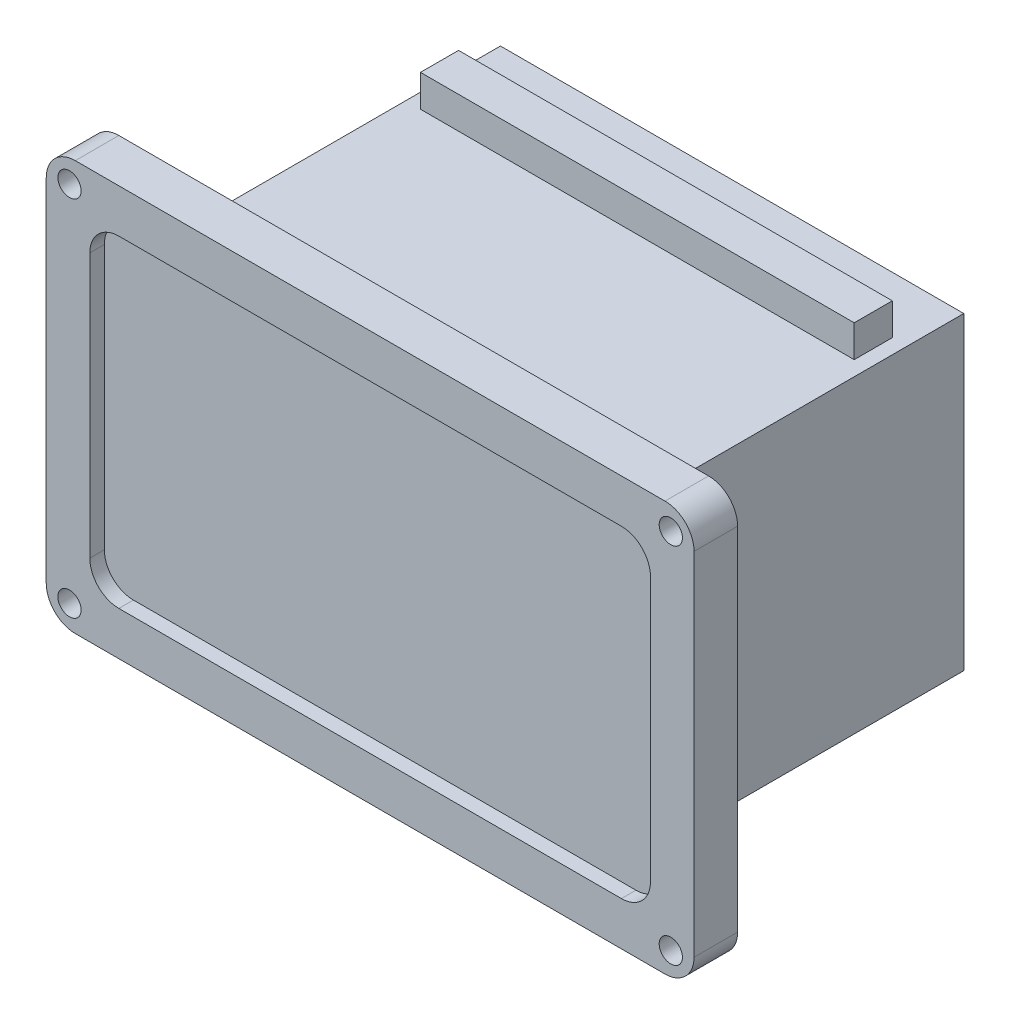
SolidWorks part; units mm, degrees
ref_plane "Alzado" through (0, 0, 0) normal (0, 0, 1) x (1, 0, 0)
ref_plane "Planta" through (0, 0, 0) normal (0, 1, 0) x (1, 0, 0)
ref_plane "Vista lateral" through (0, 0, 0) normal (1, 0, 0) x (0, 0, -1)
sketch "Croquis1" plane through (0, 0, 0) normal (0, 0, 1) x (1, 0, 0)
  line L1 (-101.5, -70.5) -> (101.5, -70.5)
  line L2 (-111.5, -60.5) -> (-111.5, 60.5)
  line L3 (-101.5, 70.5) -> (101.5, 70.5)
  line L4 (111.5, -60.5) -> (111.5, 60.5)
  line L5 (-111.5, -70.5) -> (111.5, 70.5) construction
  line L6 (-111.5, 70.5) -> (111.5, -70.5) construction
  arc A0 (-101.5, -70.5) -> (-111.5, -60.5) centre (-101.5, -60.5) cw
  arc A1 (101.5, -70.5) -> (111.5, -60.5) centre (101.5, -60.5) ccw
  arc A2 (101.5, 70.5) -> (111.5, 60.5) centre (101.5, 60.5) cw
  arc A3 (-111.5, 60.5) -> (-101.5, 70.5) centre (-101.5, 60.5) cw
  point P0 (0, 0)
  dimension "D3" = 10
  dimension "D1" = 223
  dimension "D2" = 141
extrude "Saliente-Extruir1" add sketch "Croquis1" along normal blind 15
sketch "Croquis2" plane through (0, 0, 0) normal (0, 0, -1) x (-1, 0, 0)
  line L0 (-101.5, 70.5) -> (101.5, 70.5) construction
  line L1 (-79.75, -53.25) -> (79.75, -53.25)
  line L2 (-79.75, -53.25) -> (-79.75, 53.25)
  line L3 (-79.75, 53.25) -> (79.75, 53.25)
  line L4 (79.75, -53.25) -> (79.75, 53.25)
  line L5 (-79.75, -53.25) -> (79.75, 53.25) construction
  line L6 (-79.75, 53.25) -> (79.75, -53.25) construction
  point P0 (0, 0)
  dimension "D1" = 106.5
  dimension "D2" = 159.5
  dimension "D3" = 17.25
extrude "Saliente-Extruir2" add sketch "Croquis2" along normal blind 109.6
sketch "Croquis3" plane through (0, 0, 15) normal (0, 0, 1) x (1, 0, 0)
  line L0 (-111.5, 60.5) -> (-111.5, -60.5) construction
  line L1 (86.5, -55.5) -> (-86.5, -55.5)
  line L2 (96.5, -45.5) -> (96.5, 45.5)
  line L3 (86.5, 55.5) -> (-86.5, 55.5)
  line L4 (-96.5, -45.5) -> (-96.5, 45.5)
  line L5 (96.5, -55.5) -> (-96.5, 55.5) construction
  line L6 (96.5, 55.5) -> (-96.5, -55.5) construction
  line L7 (101.5, 70.5) -> (-101.5, 70.5) construction
  arc A0 (-86.5, -55.5) -> (-96.5, -45.5) centre (-86.5, -45.5) cw
  arc A1 (86.5, -55.5) -> (96.5, -45.5) centre (86.5, -45.5) ccw
  arc A2 (96.5, 45.5) -> (86.5, 55.5) centre (86.5, 45.5) ccw
  arc A3 (-86.5, 55.5) -> (-96.5, 45.5) centre (-86.5, 45.5) ccw
  point P0 (0, 0)
  dimension "D3" = 10
  dimension "D1" = 15
  dimension "D2" = 15
extrude "Cortar-Extruir1" cut sketch "Croquis3" against normal blind 5
sketch "Croquis4" plane through (0, 0, 15) normal (0, 0, 1) x (1, 0, 0)
  line L0 (0, 0) -> (-143.5809, 0) construction
  line L1 (0, 0) -> (0, 70.5) construction
  line L2 (101.5, 70.5) -> (-101.5, 70.5) construction
  circle A0 centre (-103.5, 62.5) radius 4
  circle A1 centre (103.5, 62.5) radius 4
  circle A2 centre (103.5, -62.5) radius 4
  circle A3 centre (-103.5, -62.5) radius 4
  dimension "D3" = 8
  dimension "D4" = 8
  dimension "D1" = 62.5
  dimension "D2" = 103.5
extrude "Cortar-Extruir2" cut sketch "Croquis4" against normal blind 15
sketch "Croquis5" plane through (0, 53.25, 0) normal (0, 1, 0) x (1, 0, 0)
  line L1 (-74.6572, 76.9808) -> (74.6572, 76.9808)
  line L2 (-74.6572, 76.9808) -> (-74.6572, 90.0913)
  line L3 (-74.6572, 90.0913) -> (74.6572, 90.0913)
  line L4 (74.6572, 76.9808) -> (74.6572, 90.0913)
  line L5 (-74.6572, 76.9808) -> (74.6572, 90.0913) construction
  line L6 (-74.6572, 90.0913) -> (74.6572, 76.9808) construction
  point P0 (0, 83.5361)
extrude "Saliente-Extruir3" add sketch "Croquis5" along normal blind 11
